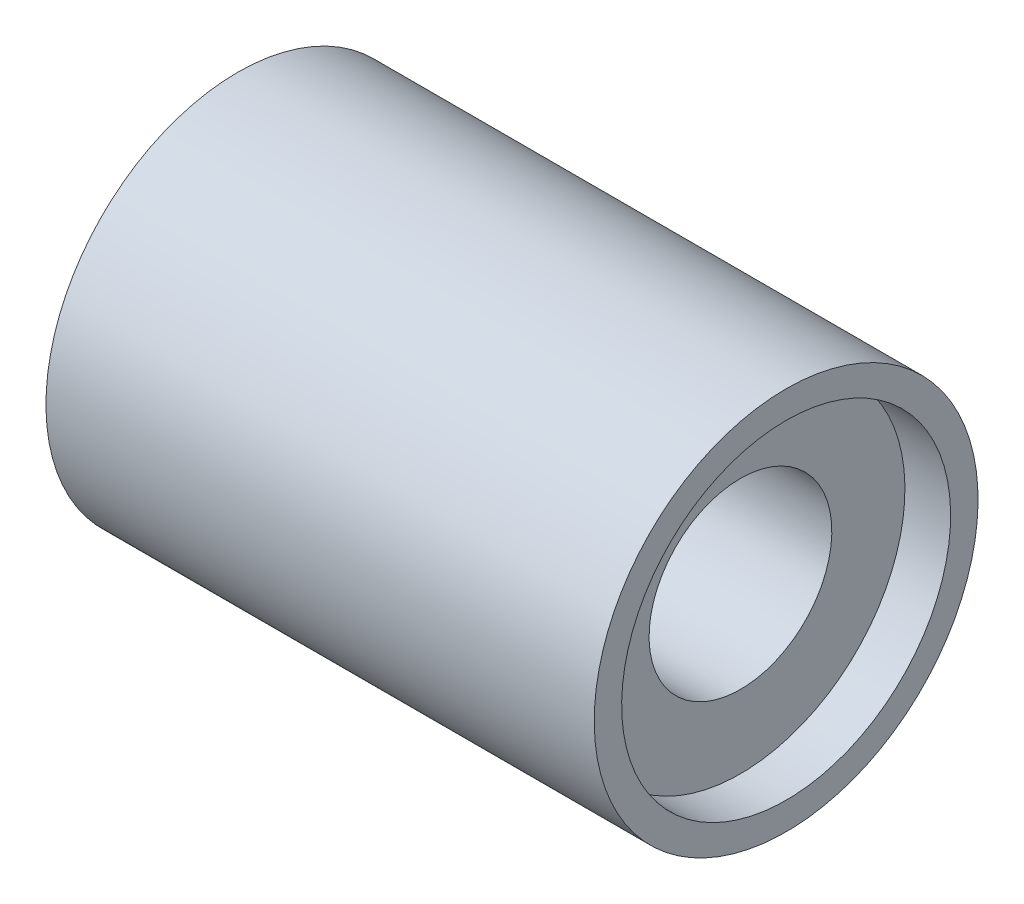
SolidWorks part; units mm, degrees
material "Ст3сп ГОСТ 535-2005"
ref_plane "Plano frontal" through (0, 0, 0) normal (0, 0, 1) x (1, 0, 0)
ref_plane "Plano superior" through (0, 0, 0) normal (0, 1, 0) x (1, 0, 0)
ref_plane "Plano direito" through (0, 0, 0) normal (1, 0, 0) x (0, 0, -1)
sketch "Esboço1" plane through (0, 0, 0) normal (0, 0, 1) x (1, 0, 0)
  line L0 (-6, 4.2) -> (6, 4.2)
  line L9 (6, 4.2) -> (6, 3.6)
  line L10 (5, 2) -> (-5, 2)
  line L12 (0, 2) -> (0, 0) construction
  line L13 (0, 0) -> (-86.5, 0) construction
  line L14 (-6, 3) -> (-6, 4.2)
  line L15 (-6, 3) -> (-5, 3)
  line L17 (-5, 3) -> (-5, 2)
  line L19 (6, 3.6) -> (5, 3.6)
  line L22 (5, 3.6) -> (5, 2)
  dimension "D1" = 10
  dimension "D2" = 0.6
  dimension "D3" = 12
  dimension "D4" = 4
  dimension "D5" = 4.2
  dimension "D7" = 1
  dimension "D8" = 1
  dimension "D9" = 1
revolve "Revolução1" add sketch "Esboço1" angle 360 about L13
